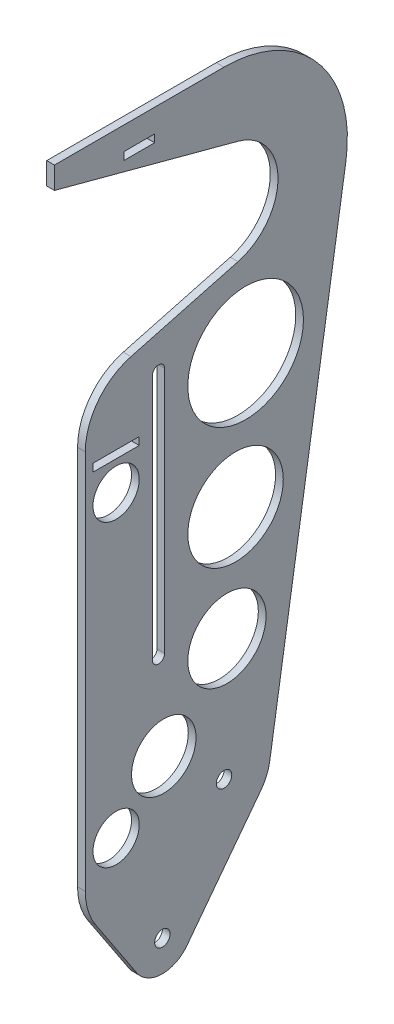
SolidWorks part; units mm, degrees
material "6061-T6 (SS)"
ref_plane "Front Plane" through (0, 0, 0) normal (0, 0, 1) x (1, 0, 0)
ref_plane "Top Plane" through (0, 0, 0) normal (0, 1, 0) x (1, 0, 0)
ref_plane "Right Plane" through (0, 0, 0) normal (1, 0, 0) x (0, 0, -1)
sketch "Sketch1" plane through (0, 0, 0) normal (1, 0, 0) x (0, 0, -1)
  line L0 (0, 0) -> (-25.4, -43.9941) construction
  line L1 (-69.85, 244.9253) -> (5.7523, 224.6677)
  line L2 (-69.85, 244.9253) -> (-69.85, 254)
  line L3 (-15.2815, -51.6691) -> (15.1778, -11.5125)
  line L4 (18.816, -2.9766) -> (50.1761, 195.2625)
  line L5 (-35.9888, -51.006) -> (-52.9277, -25.4263)
  line L6 (5.7523, 181.7323) -> (-38.324, 169.9221)
  line L7 (-57.15, -11.4025) -> (-57.15, 145.3876)
  line L10 (-69.85, 254) -> (0, 254)
  line L12 (-26.9875, 158.75) -> (-26.9875, 57.15) construction
  line L13 (-24.4475, 158.75) -> (-24.4475, 57.15)
  line L14 (-29.5275, 158.75) -> (-29.5275, 57.15)
  circle A0 centre (0, 0) radius 3.175
  circle A1 centre (-25.4, -43.9941) radius 3.175
  arc A3 (5.7523, 224.6677) -> (5.7523, 181.7323) centre (0, 203.2) cw
  arc A4 (-15.2815, -51.6691) -> (-35.9888, -51.006) centre (-25.4, -43.9941) cw
  arc A5 (0, 254) -> (50.1761, 195.2625) centre (0, 203.2) cw
  arc A6 (15.1778, -11.5125) -> (18.816, -2.9766) centre (0, 0) ccw
  arc A7 (-57.15, 145.3876) -> (-38.324, 169.9221) centre (-31.75, 145.3876) cw
  arc A8 (-24.4475, 158.75) -> (-29.5275, 158.75) centre (-26.9875, 158.75) ccw
  arc A9 (-29.5275, 57.15) -> (-24.4475, 57.15) centre (-26.9875, 57.15) ccw
  arc A10 (-52.9277, -25.4263) -> (-57.15, -11.4025) centre (-31.75, -11.4025) cw
  point P5 (-26.9875, 107.95)
  point P20 (0, 0)
  point P26 (-54.7303, -11.5125)
  point P28 (0, 0)
  point P29 (-57.15, -19.05)
  point P30 (-57.6259, 247.65)
  point P31 (-80.8823, 247.8814)
  point P33 (-57.15, 164.8777)
  dimension "D1" = 6.35
  dimension "D2" = 50.8
  dimension "D3" = 203.2
  dimension "D4" = 19.05
  dimension "D6" = 6.35
  dimension "D7" = 12.7
  dimension "D8" = 80.0476
  dimension "D9" = 22.225
  dimension "D10" = 12.7
  dimension "D11" = 50.8
  dimension "D15" = 25.4
  dimension "D17" = 25.4
  dimension "D5" = 30
  dimension "D12" = 15
  dimension "D13" = 15
  dimension "D14" = 57.15
  dimension "D16" = 5.08
  dimension "25" = 30.1625
  dimension "D18" = 158.75
  dimension "D19" = 57.15
  dimension "D20" = 19.05
extrude "Boss-Extrude1" add sketch "Sketch1" along normal blind 3.175
sketch "Sketch2" plane through (0, 0, 0) normal (-1, 0, 0) x (0, 0, 1)
  line L0 (57.15, 145.3876) -> (57.15, -11.4025) construction
  line L1 (53.975, 139.7) -> (34.925, 139.7)
  line L2 (53.975, 139.7) -> (53.975, 136.525)
  line L3 (53.975, 136.525) -> (34.925, 136.525)
  line L4 (34.925, 139.7) -> (34.925, 136.525)
  line L5 (69.85, 254) -> (69.85, 244.9253) construction
  line L6 (41.275, 241.3) -> (28.575, 241.3)
  line L7 (41.275, 241.3) -> (41.275, 244.475)
  line L8 (41.275, 244.475) -> (28.575, 244.475)
  line L9 (28.575, 241.3) -> (28.575, 244.475)
  circle A0 centre (0, 0) radius 3.175 construction
  point P15 (41.275, 240.7149)
  point P16 (41.275, 244.1073)
  dimension "D1" = 3.175
  dimension "D2" = 19.05
  dimension "D3" = 3.175
  dimension "D4" = 139.7
  dimension "D5" = 241.3
  dimension "D6" = 3.175
  dimension "D7" = 28.575
  dimension "D8" = 12.7
extrude "Cut-Extrude1" cut sketch "Sketch2" against normal through all
sketch "Sketch3" plane through (3.175, 0, 0) normal (1, 0, 0) x (0, 0, -1)
  line L0 (18.816, -2.9766) -> (50.1761, 195.2625) construction
  line L1 (-24.4475, 57.15) -> (-24.4475, 158.75) construction
  line L2 (5.7523, 181.7323) -> (-38.324, 169.9221) construction
  line L4 (-57.15, 145.3876) -> (-57.15, -11.4025) construction
  circle A0 centre (8.8881, 147.6128) radius 23.8106
  circle A1 centre (4.7352, 94.7825) radius 19.6577
  circle A2 centre (1.1859, 49.6306) radius 16.1084
  circle A3 centre (-24.8267, 20.6984) radius 13.2733
  circle A4 centre (0, 0) radius 19.05 construction
  arc A5 (15.1778, -11.5125) -> (18.816, -2.9766) centre (0, 0) ccw construction
  dimension "D1" = 9.525
  dimension "D2" = 9.525
  dimension "D3" = 9.525
  dimension "D4" = 9.525
  dimension "D5" = 9.525
  dimension "D6" = 9.525
  dimension "D7" = 9.958
  dimension "D8" = 9.525
  dimension "D9" = 9.525
  dimension "D10" = 9.525
  dimension "D12" = 19.05
extrude "Cut-Extrude2" cut sketch "Sketch3" against normal through all
sketch "Sketch4" plane through (3.175, 0, 0) normal (1, 0, 0) x (0, 0, -1)
  circle A0 centre (-44.45, 124.46) radius 9.525
  circle A1 centre (-44.45, 1.27) radius 9.525
  point P4 (0, 0)
  dimension "D1" = 19.05
  dimension "D2" = 44.45
  dimension "D3" = 124.46
  dimension "D4" = 1.27
extrude "Cut-Extrude3" cut sketch "Sketch4" against normal through all
